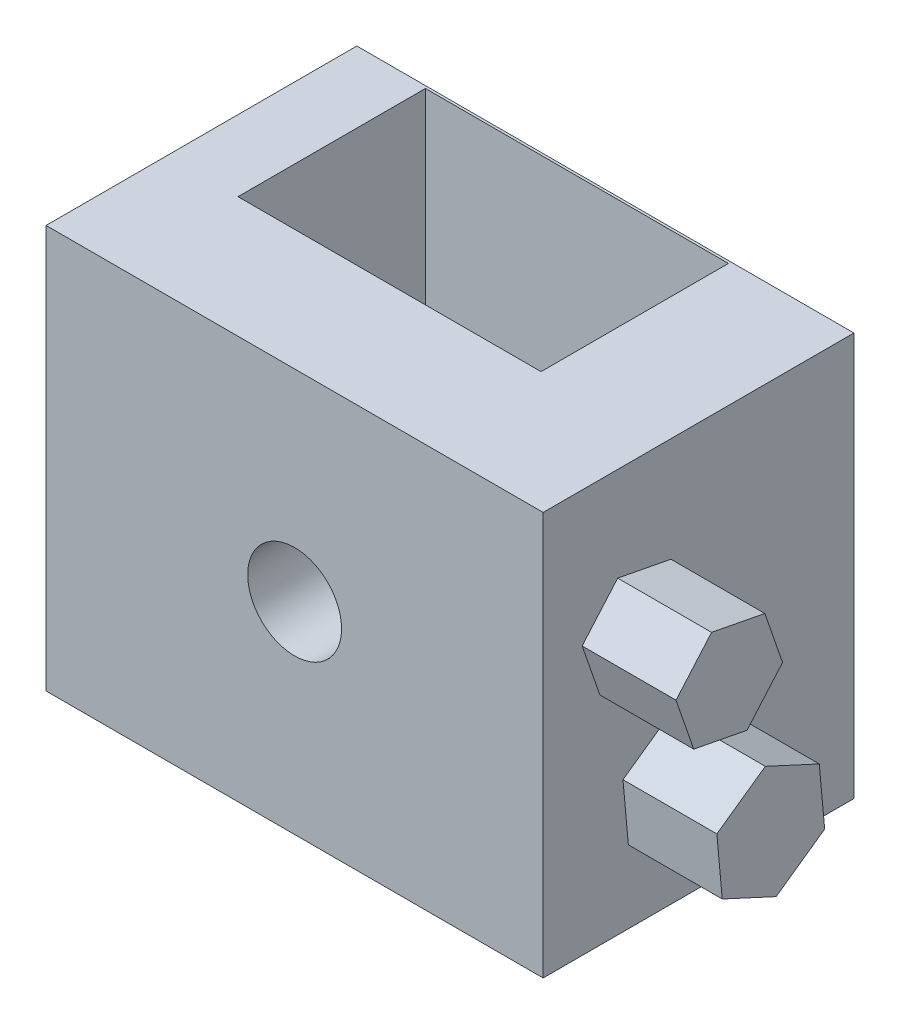
SolidWorks part; units mm, degrees
ref_plane "Front Plane" through (0, 0, 0) normal (0, 0, 1) x (1, 0, 0)
ref_plane "Top Plane" through (0, 0, 0) normal (0, 1, 0) x (1, 0, 0)
ref_plane "Right Plane" through (0, 0, 0) normal (1, 0, 0) x (0, 0, -1)
sketch "Sketch2" plane through (0, 0, 0) normal (0, 0, 1) x (1, 0, 0)
  line L1 (-67.2388, -54.5382) -> (67.2388, -54.5382)
  line L2 (-67.2388, -54.5382) -> (-67.2388, 54.5382)
  line L3 (-67.2388, 54.5382) -> (67.2388, 54.5382)
  line L4 (67.2388, -54.5382) -> (67.2388, 54.5382)
  line L5 (-67.2388, -54.5382) -> (67.2388, 54.5382) construction
  line L6 (-67.2388, 54.5382) -> (67.2388, -54.5382) construction
  point P0 (0, 0)
extrude "Boss-Extrude1" add sketch "Sketch2" along normal blind 84.074
sketch "Sketch3" plane through (0, 0, 84.074) normal (0, 0, 1) x (1, 0, 0)
  circle A0 centre (0, 0) radius 12.7
  dimension "D1" = 25.4
extrude "Cut-Extrude1" cut sketch "Sketch3" against normal blind 127
sketch "Sketch4" plane through (0, 54.5382, 0) normal (0, 1, 0) x (1, 0, 0)
  line L1 (-48.013, -0.6681) -> (33.9651, -0.6681)
  line L2 (-48.013, -0.6681) -> (-48.013, -51.3752)
  line L3 (-48.013, -51.3752) -> (33.9651, -51.3752)
  line L4 (33.9651, -0.6681) -> (33.9651, -51.3752)
extrude "Cut-Extrude2" cut sketch "Sketch4" against normal blind 104.14
sketch "Sketch5" plane through (67.2388, 0, 0) normal (1, 0, 0) x (0, 0, -1)
  line L1 (-54.3263, 1.3258) -> (-44.7111, 12.412)
  line L2 (-44.7111, 12.412) -> (-49.5045, 26.2821)
  line L3 (-49.5045, 26.2821) -> (-63.913, 29.066)
  line L4 (-63.913, 29.066) -> (-73.5282, 17.9798)
  line L5 (-73.5282, 17.9798) -> (-68.7349, 4.1097)
  line L6 (-68.7349, 4.1097) -> (-54.3263, 1.3258)
  circle A0 centre (-59.1197, 15.1959) radius 12.7089 construction
extrude "Boss-Extrude2" add sketch "Sketch5" along normal blind 25.4
sketch "Sketch6" plane through (67.2388, 0, 0) normal (1, 0, 0) x (0, 0, -1)
  line L1 (-33.3172, -32.3296) -> (-34.7799, -16.3339)
  line L2 (-34.7799, -16.3339) -> (-49.3639, -9.6028)
  line L3 (-49.3639, -9.6028) -> (-62.4852, -18.8674)
  line L4 (-62.4852, -18.8674) -> (-61.0225, -34.8631)
  line L5 (-61.0225, -34.8631) -> (-46.4385, -41.5942)
  line L6 (-46.4385, -41.5942) -> (-33.3172, -32.3296)
  circle A0 centre (-47.9012, -25.5985) radius 13.9104 construction
extrude "Boss-Extrude3" add sketch "Sketch6" along normal blind 25.4
